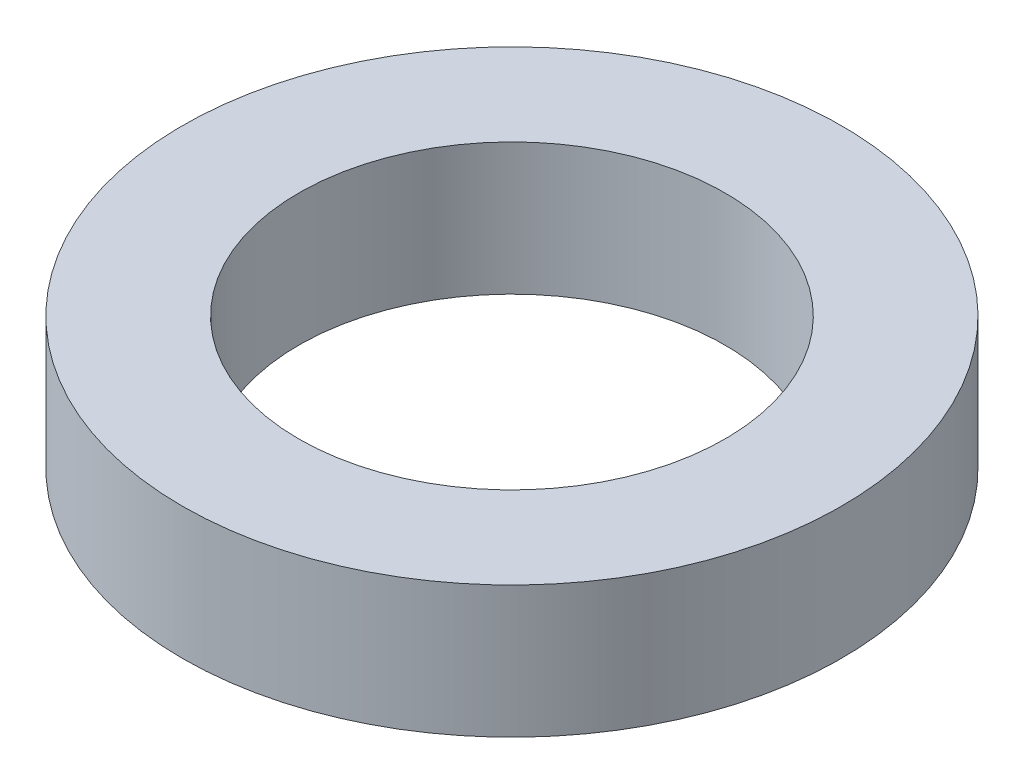
SolidWorks part; units mm, degrees
ref_plane "Front Plane" through (0, 0, 0) normal (0, 0, 1) x (1, 0, 0)
ref_plane "Top Plane" through (0, 0, 0) normal (0, 1, 0) x (1, 0, 0)
ref_plane "Right Plane" through (0, 0, 0) normal (1, 0, 0) x (0, 0, -1)
sketch "Sketch1" plane through (0, 0, 0) normal (0, 1, 0) x (1, 0, 0)
  circle A0 centre (0, 0) radius 9.525
  circle A1 centre (0, 0) radius 6.1595
  dimension "D1" = 19.05
  dimension "D2" = 12.319
extrude "Boss-Extrude1" add sketch "Sketch1" along normal blind 3.81
